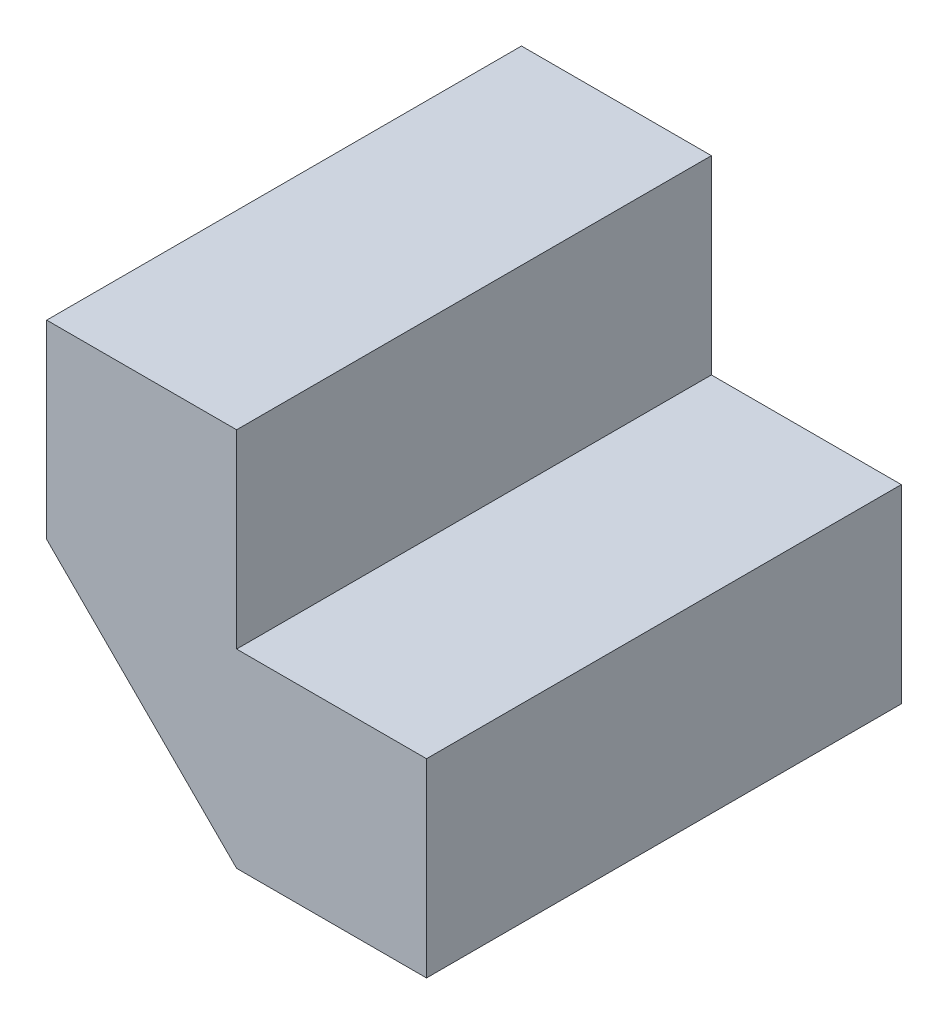
SolidWorks part; units mm, degrees
ref_plane "Front Plane" through (0, 0, 0) normal (0, 0, 1) x (1, 0, 0)
ref_plane "Top Plane" through (0, 0, 0) normal (0, 1, 0) x (1, 0, 0)
ref_plane "Right Plane" through (0, 0, 0) normal (1, 0, 0) x (0, 0, -1)
sketch "Sketch1" plane through (0, 0, 0) normal (0, 0, 1) x (1, 0, 0)
  line L0 (-20, 20) -> (-10, 20)
  line L1 (-10, 20) -> (-10, 10)
  line L2 (-10, 10) -> (0, 10)
  line L3 (0, 10) -> (0, 0)
  line L4 (0, 0) -> (-10, 0)
  line L5 (-10, 0) -> (-20, 10)
  line L6 (-20, 10) -> (-20, 20)
  point P2 (-20, 0)
  dimension "D1" = 10
  dimension "D2" = 10
  dimension "D3" = 10
  dimension "D4" = 10
  dimension "D5" = 10
  dimension "D6" = 10
  dimension "D7" = 10
extrude "Boss-Extrude1" add sketch "Sketch1" along normal blind 25
